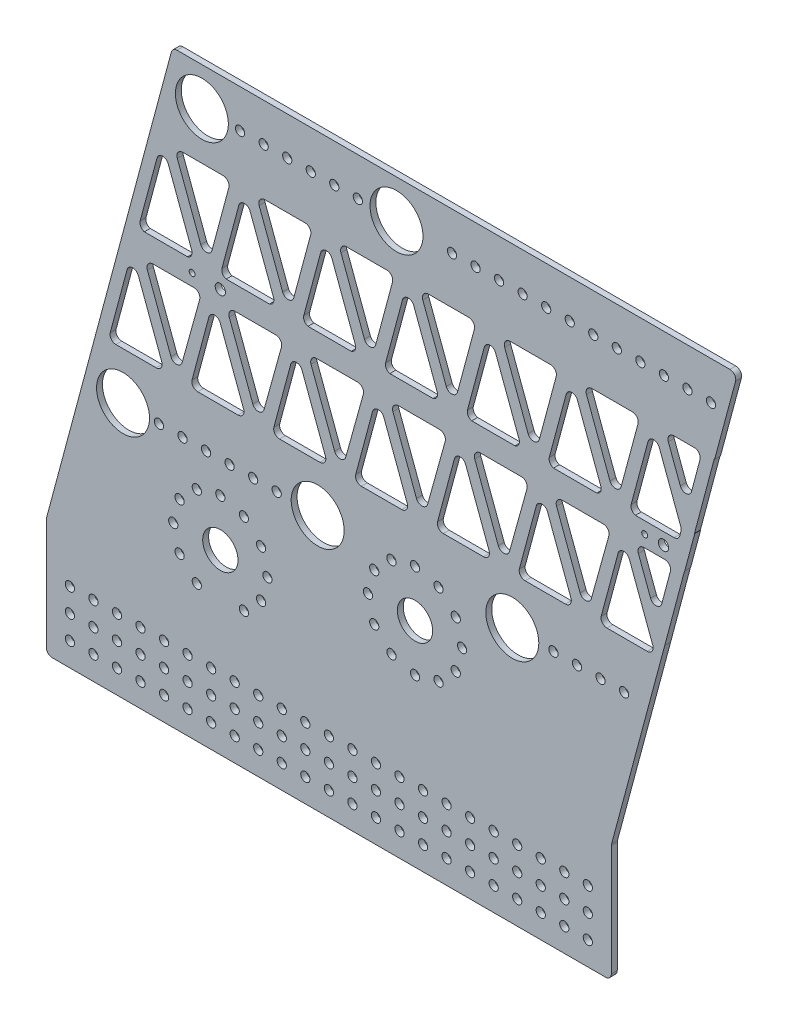
SolidWorks part; units mm, degrees
other "Markup1"
sketch "Sketch5" plane through (358.3965, -117.475, 3.175) normal (0.0852, -0.0535, 0.9949) x (0.9831, -0.1579, -0.0927)
ref_plane "Front Plane" through (0, 0, 0) normal (0, 0, 1) x (1, 0, 0)
ref_plane "Top Plane" through (0, 0, 0) normal (0, 1, 0) x (1, 0, 0)
ref_plane "Right Plane" through (0, 0, 0) normal (1, 0, 0) x (0, 0, -1)
sketch "Sketch1" plane through (0, 0, 0) normal (0, 0, 1) x (1, 0, 0)
  line L0 (0, 0) -> (53.5965, 200.025)
  line L2 (53.5965, 200.025) -> (358.3965, 200.025)
  line L3 (358.3965, 200.025) -> (304.8, 0)
  line L4 (304.8, 0) -> (0, 0)
  line L6 (69.4322, 193.675) -> (69.4322, 200.025) construction
  line L8 (26.7983, 100.0125) -> (331.5983, 100.0125) construction
  line L9 (26.8953, 6.35) -> (26.8953, 0) construction
  line L10 (69.4322, 179.3875) -> (174.4104, 179.3875) construction
  line L11 (26.8953, 20.6375) -> (131.8953, 20.6375) construction
  line L12 (0, 0) -> (-14.4626, -53.975)
  line L13 (-14.4626, -53.975) -> (290.3374, -53.975)
  line L14 (290.3374, -53.975) -> (304.8, 0)
  line L15 (55.6316, 183.0854) -> (49.498, 184.7289) construction
  line L16 (69.4322, 179.3875) -> (184.3953, -2.2949) construction
  line L17 (13.0946, 24.3354) -> (6.961, 25.9789) construction
  line L18 (55.6316, 183.0854) -> (69.4322, 179.3875) construction
  line L19 (26.8953, 20.6375) -> (79.3953, -21.7889) construction
  line L20 (-14.4626, -53.975) -> (-14.4626, -117.475)
  line L21 (-14.4626, -117.475) -> (290.3374, -117.475)
  line L22 (290.3374, -117.475) -> (290.3374, -53.975)
  line L23 (-1.7626, -79.375) -> (10.9374, -79.375) construction
  line L24 (-1.7626, -79.375) -> (-1.7626, -92.075) construction
  line L25 (79.3953, 20.6375) -> (79.3953, -25.072) construction
  line L26 (131.8953, 20.6375) -> (236.8953, 20.6375) construction
  line L27 (184.3953, 20.6375) -> (184.3953, -150.5418) construction
  circle A0 centre (69.4322, 179.3875) radius 14.2875
  circle A2 centre (69.4322, 179.3875) radius 25.4 construction
  circle A3 centre (26.8953, 20.6375) radius 14.2875
  circle A4 centre (174.4104, 179.3875) radius 14.2875
  circle A5 centre (279.3886, 179.3875) radius 14.2875 construction
  circle A6 centre (131.8953, 20.6375) radius 14.2875
  circle A7 centre (236.8953, 20.6375) radius 14.2875
  circle A8 centre (79.3953, -21.7889) radius 9.525
  circle A9 centre (184.3953, -2.2949) radius 9.525
  circle A10 centre (26.8953, 20.6375) radius 25.4 construction
  circle A11 centre (-1.7626, -79.375) radius 2.4892
  circle A12 centre (10.9374, -79.375) radius 2.4892
  circle A13 centre (23.6374, -79.375) radius 2.4892
  circle A14 centre (36.3374, -79.375) radius 2.4892
  circle A15 centre (49.0374, -79.375) radius 2.4892
  circle A16 centre (61.7374, -79.375) radius 2.4892
  circle A17 centre (74.4374, -79.375) radius 2.4892
  circle A18 centre (87.1374, -79.375) radius 2.4892
  circle A19 centre (99.8374, -79.375) radius 2.4892
  circle A20 centre (112.5374, -79.375) radius 2.4892
  circle A21 centre (125.2374, -79.375) radius 2.4892
  circle A22 centre (137.9374, -79.375) radius 2.4892
  circle A23 centre (150.6374, -79.375) radius 2.4892
  circle A24 centre (163.3374, -79.375) radius 2.4892
  circle A25 centre (176.0374, -79.375) radius 2.4892
  circle A26 centre (188.7374, -79.375) radius 2.4892
  circle A27 centre (201.4374, -79.375) radius 2.4892
  circle A28 centre (214.1374, -79.375) radius 2.4892
  circle A29 centre (226.8374, -79.375) radius 2.4892
  circle A30 centre (239.5374, -79.375) radius 2.4892
  circle A31 centre (252.2374, -79.375) radius 2.4892
  circle A32 centre (264.9374, -79.375) radius 2.4892
  circle A33 centre (277.6374, -79.375) radius 2.4892
  circle A34 centre (10.9374, -92.075) radius 2.4892
  circle A35 centre (23.6374, -92.075) radius 2.4892
  circle A36 centre (36.3374, -92.075) radius 2.4892
  circle A37 centre (49.0374, -92.075) radius 2.4892
  circle A38 centre (61.7374, -92.075) radius 2.4892
  circle A39 centre (74.4374, -92.075) radius 2.4892
  circle A40 centre (87.1374, -92.075) radius 2.4892
  circle A41 centre (99.8374, -92.075) radius 2.4892
  circle A42 centre (112.5374, -92.075) radius 2.4892
  circle A43 centre (125.2374, -92.075) radius 2.4892
  circle A44 centre (137.9374, -92.075) radius 2.4892
  circle A45 centre (150.6374, -92.075) radius 2.4892
  circle A46 centre (163.3374, -92.075) radius 2.4892
  circle A47 centre (176.0374, -92.075) radius 2.4892
  circle A48 centre (188.7374, -92.075) radius 2.4892
  circle A49 centre (201.4374, -92.075) radius 2.4892
  circle A50 centre (214.1374, -92.075) radius 2.4892
  circle A51 centre (226.8374, -92.075) radius 2.4892
  circle A52 centre (239.5374, -92.075) radius 2.4892
  circle A53 centre (252.2374, -92.075) radius 2.4892
  circle A54 centre (264.9374, -92.075) radius 2.4892
  circle A55 centre (277.6374, -92.075) radius 2.4892
  circle A56 centre (10.9374, -104.775) radius 2.4892
  circle A57 centre (23.6374, -104.775) radius 2.4892
  circle A58 centre (36.3374, -104.775) radius 2.4892
  circle A59 centre (49.0374, -104.775) radius 2.4892
  circle A60 centre (61.7374, -104.775) radius 2.4892
  circle A61 centre (74.4374, -104.775) radius 2.4892
  circle A62 centre (87.1374, -104.775) radius 2.4892
  circle A63 centre (99.8374, -104.775) radius 2.4892
  circle A64 centre (112.5374, -104.775) radius 2.4892
  circle A65 centre (125.2374, -104.775) radius 2.4892
  circle A66 centre (137.9374, -104.775) radius 2.4892
  circle A67 centre (150.6374, -104.775) radius 2.4892
  circle A68 centre (163.3374, -104.775) radius 2.4892
  circle A69 centre (176.0374, -104.775) radius 2.4892
  circle A70 centre (188.7374, -104.775) radius 2.4892
  circle A71 centre (201.4374, -104.775) radius 2.4892
  circle A72 centre (214.1374, -104.775) radius 2.4892
  circle A73 centre (226.8374, -104.775) radius 2.4892
  circle A74 centre (239.5374, -104.775) radius 2.4892
  circle A75 centre (252.2374, -104.775) radius 2.4892
  circle A76 centre (264.9374, -104.775) radius 2.4892
  circle A77 centre (277.6374, -104.775) radius 2.4892
  circle A78 centre (-1.7626, -92.075) radius 2.4892
  circle A79 centre (-1.7626, -104.775) radius 2.4892
  circle A80 centre (79.3953, -21.7889) radius 31.75 construction
  circle A81 centre (131.8953, 20.6375) radius 25.4 construction
  circle A82 centre (184.3953, -2.2949) radius 31.75 construction
  dimension "D1" = 304.8
  dimension "D2" = 28.575
  dimension "D3" = 50.8
  dimension "D5" = 6.35
  dimension "D15" = 19.05
  dimension "D11" = 67.5
  dimension "D20" = 63.5
  dimension "D21" = 25.4
  dimension "D23" = 4.9784
  dimension "D16" = 63.5
  dimension "D4" = 6.35
  dimension "D6" = 158.75
  dimension "D7" = 6.35
  dimension "D8" = 3
  dimension "D9" = 104.9782
  dimension "D10" = 105
  dimension "D13" = 105
  dimension "D14" = 53.975
  dimension "D18" = 215
  dimension "D19" = 6.35
  dimension "D22" = 12.7
  dimension "D26" = 90
  dimension "D27" = 12.7
  dimension "D28" = 12.7
  dimension "D12" = 3
  dimension "D24" = 23
  dimension "D25" = 3
extrude "Boss-Extrude3" add sketch "Sketch1" along normal blind 3.175 contours L4 L3 L2 L0 A7 A6 A5 A4 A3 A0 | L13 L14 L4 L12 | L21 L22 L13 L20 A79 A78 A77 A76 A75 A74 A73 A72 A71 A70 A69 A68 A67 A66 A65 A64 A63 A62 A61 A60 A59 A58 A57
ref_plane "Plane1" through (0, 0, -60.325) normal (0, 0, -1) x (-1, 0, 0)
sketch "Sketch4" plane through (0, 0, 3.175) normal (0, 0, 1) x (1, 0, 0)
  line L0 (23.0475, 46.0375) -> (44.8208, 46.0375)
  line L1 (-14.4626, -53.975) -> (53.5965, 200.025) construction
  line L2 (358.3965, 200.025) -> (290.3374, -53.975) construction
  line L3 (41.2608, 153.9875) -> (346.0608, 153.9875) construction
  line L4 (28.4997, 106.3625) -> (333.2997, 106.3625)
  line L5 (43.0149, 93.6625) -> (65.1908, 93.6625)
  line L6 (193.6608, 153.9875) -> (193.6608, 46.0375) construction
  line L7 (19.9806, 50.0343) -> (29.0965, 84.0551)
  line L8 (35.139, 84.3405) -> (47.7965, 50.3196)
  line L9 (40.0392, 89.3804) -> (52.7475, 55.2231)
  line L10 (58.7828, 55.4822) -> (68.2505, 89.6394)
  line L11 (39.1851, 106.264) -> (60.9585, 106.264)
  line L12 (59.1526, 153.889) -> (80.926, 153.889)
  line L13 (36.1183, 110.2608) -> (45.2342, 144.2817)
  line L14 (51.2767, 144.567) -> (63.9342, 110.5462)
  line L15 (56.1769, 149.6069) -> (68.8344, 115.586)
  line L16 (74.8769, 115.8714) -> (83.9928, 149.8923)
  line L17 (62.8389, 46.3426) -> (75.955, 93.6625)
  line L18 (75.955, 93.6625) -> (93.3189, 46.3426)
  line L19 (93.3189, 46.3426) -> (62.8389, 46.3426)
  circle A0 centre (26.8953, 20.6375) radius 14.2875 construction
  circle A1 centre (69.4322, 179.3875) radius 14.2875 construction
  arc A2 (40.0392, 89.3804) -> (43.0149, 93.6625) centre (43.0149, 90.4875) cw
  arc A3 (68.2505, 89.6394) -> (65.1908, 93.6625) centre (65.1908, 90.4875) ccw
  arc A4 (52.7475, 55.2231) -> (58.7828, 55.4822) centre (55.7232, 56.3302) ccw
  arc A5 (44.8208, 46.0375) -> (47.7965, 50.3196) centre (44.8208, 49.2125) ccw
  arc A6 (19.9806, 50.0343) -> (23.0475, 46.0375) centre (23.0475, 49.2125) ccw
  arc A7 (29.0965, 84.0551) -> (35.139, 84.3405) centre (32.1633, 83.2334) cw
  arc A8 (56.1769, 149.6069) -> (59.1526, 153.889) centre (59.1526, 150.714) cw
  arc A9 (83.9928, 149.8923) -> (80.926, 153.889) centre (80.926, 150.714) ccw
  arc A10 (68.8344, 115.586) -> (74.8769, 115.8714) centre (71.8101, 116.6931) ccw
  arc A11 (60.9585, 106.264) -> (63.9342, 110.5462) centre (60.9585, 109.439) ccw
  arc A12 (36.1183, 110.2608) -> (39.1851, 106.264) centre (39.1851, 109.439) ccw
  arc A13 (45.2342, 144.2817) -> (51.2767, 144.567) centre (48.301, 143.4599) cw
  point P18 (193.6608, 100.0125)
  point P29 (56.165, 46.0375)
  point P34 (31.6708, 93.6625)
  dimension "D1" = 25.4
  dimension "D8" = 3.175
  dimension "D9" = 3.175
  dimension "D2" = 25.4
  dimension "D3" = 12.7
  dimension "D4" = 6.35
  dimension "D5" = 6.35
  dimension "D6" = 6.35
  dimension "D7" = 6.35
  dimension "D10" = 6.35
  dimension "D11" = 30.48
  dimension "D12" = 6.35
extrude "Cut-Extrude5" cut sketch "Sketch4" against normal through all contours A13 L13 A12 L4 A11 L14 | L15 A10 L16 A9 L12 A8 | L9 A4 L10 A3 L5 A2 | A7 L7 A6 L0 A5 L8
pattern_linear "LPattern10" count 7 spacing 44.1452 along (1, 0, 0) of "Cut-Extrude5"
sketch "Sketch6" plane through (0, 0, 3.175) normal (0, 0, 1) x (1, 0, 0)
  line L0 (319.1377, 53.5091) -> (345.7972, 153.889)
  line L1 (313.0005, 55.1391) -> (339.6599, 155.519)
  line L2 (339.6599, 155.519) -> (345.7972, 153.889)
  line L3 (313.0005, 55.1391) -> (319.1377, 53.5091)
  dimension "D1" = 6.35
extrude "Boss-Extrude4" add sketch "Sketch6" against normal blind 3.175
fillet "Fillet3" radius 3.175 6 edges at (314.937, 62.4307, 1.5875) (323.2317, 93.6625, 1.5875) (330.9916, 122.8806, 1.5875) (328.1696, 112.255, 1.5875) (326.6047, 106.3625, 1.5875) (339.227, 153.889, 1.5875)
sketch "Sketch2" plane through (0, 0, 3.175) normal (0, 0, 1) x (1, 0, 0)
  line L0 (79.3953, -21.7889) -> (79.3953, 3.6111) construction
  line L1 (184.3953, -2.2949) -> (184.3953, -27.6949) construction
  line L2 (184.3953, -2.2949) -> (171.6953, -24.2919) construction
  line L3 (69.4322, 179.3875) -> (69.4322, 20.6375) construction
  line L4 (43.7978, 20.6375) -> (41.1828, 20.6375) construction
  line L5 (131.8953, 20.6375) -> (69.4322, 20.6375) construction
  line L6 (46.287, 20.6375) -> (58.987, 20.6375) construction
  line L7 (90.0697, 179.3875) -> (102.7697, 179.3875) construction
  line L8 (319.1377, 53.5091) -> (290.3374, -53.975) construction
  line L9 (297.1818, 20.6375) -> (284.4818, 20.6375) construction
  circle A0 centre (79.3953, -21.7889) radius 31.75 construction
  circle A1 centre (79.3953, -21.7889) radius 25.4 construction
  circle A2 centre (79.3953, 3.6111) radius 2.4892
  circle A3 centre (92.0953, 0.2081) radius 2.4892
  circle A4 centre (101.3924, -9.0889) radius 2.4892
  circle A5 centre (104.7953, -21.7889) radius 2.4892
  circle A6 centre (101.3924, -34.4889) radius 2.4892
  circle A7 centre (92.0953, -43.786) radius 2.4892
  circle A9 centre (66.6953, -43.786) radius 2.4892
  circle A10 centre (57.3983, -34.4889) radius 2.4892
  circle A11 centre (53.9953, -21.7889) radius 2.4892
  circle A12 centre (57.3983, -9.0889) radius 2.4892
  circle A13 centre (66.6953, 0.2081) radius 2.4892
  circle A14 centre (79.3953, -47.1889) radius 2.4892 [skipped]
  circle A15 centre (184.3953, -2.2949) radius 25.4 construction
  circle A16 centre (184.3953, -27.6949) radius 2.4892
  circle A17 centre (171.6953, -24.2919) radius 2.4892
  circle A18 centre (162.3983, -14.9949) radius 2.4892
  circle A19 centre (158.9953, -2.2949) radius 2.4892
  circle A20 centre (162.3983, 10.4051) radius 2.4892
  circle A21 centre (171.6953, 19.7021) radius 2.4892
  circle A23 centre (197.0953, 19.7021) radius 2.4892
  circle A24 centre (206.3924, 10.4051) radius 2.4892
  circle A25 centre (209.7953, -2.2949) radius 2.4892
  circle A26 centre (206.3924, -14.9949) radius 2.4892
  circle A27 centre (197.0953, -24.2919) radius 2.4892
  circle A28 centre (184.3953, 23.1051) radius 2.4892 [skipped]
  circle A41 centre (184.3953, 23.1051) radius 2.4892
  circle A42 centre (58.987, 20.6375) radius 2.4892
  circle A43 centre (46.287, 20.6375) radius 2.4892
  circle A44 centre (26.8953, 20.6375) radius 14.2875 construction
  circle A45 centre (71.687, 20.6375) radius 2.4892
  circle A46 centre (84.387, 20.6375) radius 2.4892
  circle A47 centre (97.087, 20.6375) radius 2.4892
  circle A48 centre (109.787, 20.6375) radius 2.4892
  circle A49 centre (90.0697, 179.3875) radius 2.4892
  circle A51 centre (102.7697, 179.3875) radius 2.4892
  circle A52 centre (115.4697, 179.3875) radius 2.4892
  circle A53 centre (128.1697, 179.3875) radius 2.4892
  circle A54 centre (140.8697, 179.3875) radius 2.4892
  circle A55 centre (153.5697, 179.3875) radius 2.4892
  circle A56 centre (166.2697, 179.3875) radius 2.4892 [skipped]
  circle A57 centre (178.9697, 179.3875) radius 2.4892 [skipped]
  circle A58 centre (191.6697, 179.3875) radius 2.4892 [skipped]
  circle A59 centre (204.3697, 179.3875) radius 2.4892
  circle A60 centre (217.0697, 179.3875) radius 2.4892
  circle A61 centre (229.7697, 179.3875) radius 2.4892
  circle A62 centre (242.4697, 179.3875) radius 2.4892
  circle A63 centre (255.1697, 179.3875) radius 2.4892
  circle A64 centre (267.8697, 179.3875) radius 2.4892
  circle A65 centre (280.5697, 179.3875) radius 2.4892
  circle A66 centre (293.2697, 179.3875) radius 2.4892
  circle A67 centre (305.9697, 179.3875) radius 2.4892
  circle A68 centre (318.6697, 179.3875) radius 2.4892
  circle A69 centre (331.3697, 179.3875) radius 2.4892
  circle A70 centre (344.0697, 179.3875) radius 2.4892
  circle A71 centre (297.1818, 20.6375) radius 2.4892
  circle A72 centre (284.4818, 20.6375) radius 2.4892
  circle A73 centre (271.7818, 20.6375) radius 2.4892
  circle A74 centre (259.0818, 20.6375) radius 2.4892
  dimension "D1" = 63.5
  dimension "D2" = 50.8
  dimension "D3" = 4.9784
  dimension "D5" = 50.8
  dimension "D6" = 4.9784
  dimension "D9" = 4.9784
  dimension "D10" = 2.615
  dimension "D13" = 4.9784
  dimension "D14" = 20.6375
  dimension "D15" = 21
  dimension "D17" = 12.7
  dimension "D4" = 12
  dimension "D7" = 30
  dimension "D8" = 12
  dimension "D11" = 6
  dimension "D12" = 12.7
  dimension "D18" = 4
  dimension "D19" = 12.7
  dimension "D16" = 12.7
extrude "Cut-Extrude6" cut sketch "Sketch2" against normal through all
fillet "Fillet2" radius 3.175 6 edges at (290.3374, -117.475, 1.5875) (-14.4626, -117.475, 1.5875) (-14.4626, -53.975, 1.5875) (53.5965, 200.025, 1.5875) (358.3965, 200.025, 1.5875) (290.3374, -53.975, 1.5875)
sketch "Sketch7" plane through (0, 0, 3.175) normal (0, 0, 1) x (1, 0, 0)
  line L6 (307.8861, 93.6625) -> (319.1034, 93.6625) construction
  line L7 (335.3016, 113.8336) -> (329.8968, 93.6625) construction
  line L8 (26.8953, 20.6375) -> (131.8953, 20.6375) construction
  line L9 (79.3953, 20.6375) -> (79.3953, 106.9138) construction
  line L10 (38.4005, 106.3625) -> (61.7431, 106.3625) construction
  circle A0 centre (308.2903, 100.0125) radius 1.5875
  circle A1 centre (318.4503, 100.0125) radius 2.7781
  circle A2 centre (79.3953, 100.0125) radius 2.7781
  circle A3 centre (64.1553, 100.0125) radius 1.5875
  point P18 (0, 0)
  dimension "D1" = 3.175
  dimension "D2" = 5.5562
  dimension "D4" = 12.7
  dimension "D6" = 5.5562
  dimension "D7" = 6.35
  dimension "D8" = 15.24
  dimension "D3" = 6.35
  dimension "D5" = 10.16
extrude "Cut-Extrude7" cut sketch "Sketch7" against normal through all
